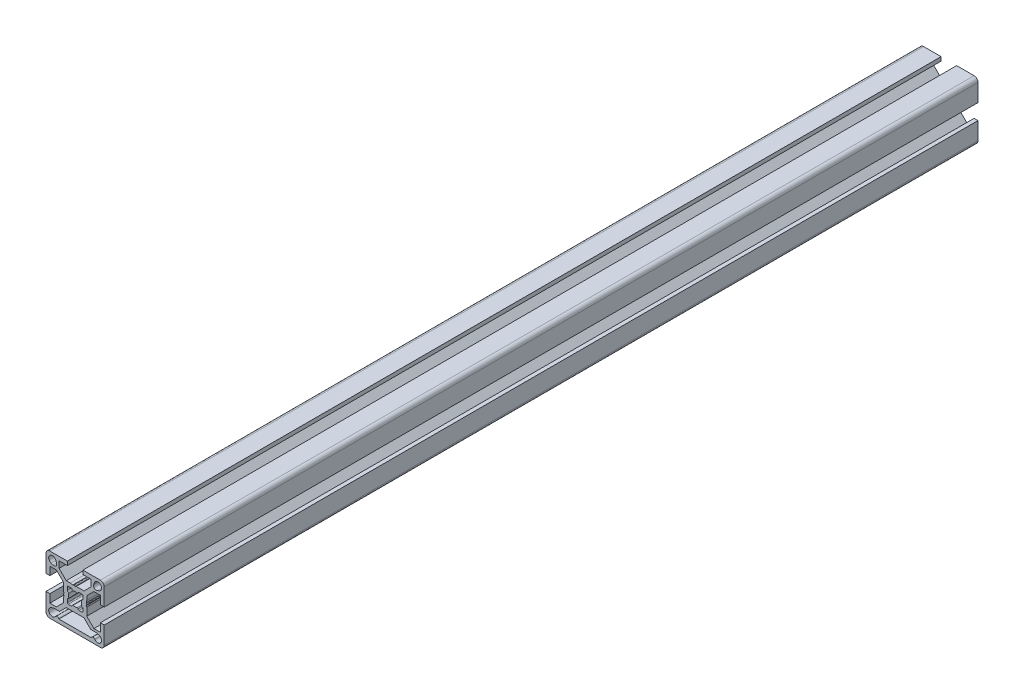
SolidWorks part; units mm, degrees
material "6063-T5"
ref_plane "Piano frontale" through (0, 0, 0) normal (0, 0, 1) x (1, 0, 0)
ref_plane "Piano superiore" through (0, 0, 0) normal (0, 1, 0) x (1, 0, 0)
ref_plane "Piano destro" through (0, 0, 0) normal (1, 0, 0) x (0, 0, -1)
ref_plane "Piano1" through (0, 0, -450) normal (0, 0, -1) x (-1, 0, 0)
sketch "Schizzo1" plane through (0, 0, -450) normal (0, 0, -1) x (-1, 0, 0)
  line L0 (12.3498, 9.9146) -> (11.3422, 9.5479)
  line L1 (9.5479, 11.3422) -> (9.9146, 12.3498)
  line L2 (-4.58, -6) -> (4.58, -6)
  line L3 (8.03, -9.45) -> (11.1, -9.45)
  line L4 (11.1, -9.45) -> (12.3619, -9.919)
  line L5 (8.3553, -13) -> (-8.3553, -13)
  line L6 (-12.3619, -9.919) -> (-11.1, -9.45)
  line L7 (-11.1, -9.45) -> (-8.03, -9.45)
  line L8 (-11.3422, 9.5479) -> (-12.3498, 9.9146)
  line L9 (-9.9146, 12.3498) -> (-9.5479, 11.3422)
  line L10 (4, 3.5) -> (4, 2)
  line L11 (4, -2) -> (4, -3.5)
  line L12 (3.5, -4) -> (2, -4)
  line L13 (-2, -4) -> (-3.5, -4)
  line L14 (-4, -3.5) -> (-4, -2)
  line L15 (-4, 2) -> (-4, 3.5)
  line L16 (-3.5, 4) -> (-2, 4)
  line L17 (2, 4) -> (3.5, 4)
  line L18 (-15, -4) -> (-15, -13)
  line L19 (-13, -15) -> (13, -15)
  line L20 (15, -13) -> (15, -4)
  line L21 (15, -4) -> (13, -4)
  line L22 (13, -4) -> (13, -8.25)
  line L23 (13, -8.25) -> (9.6642, -8.25)
  line L24 (6, -4.5858) -> (6, -2.5)
  line L25 (6, -2.5) -> (5.751, -1.2189)
  line L26 (5.751, -1.2189) -> (5.933, -0.9036)
  line L27 (5.933, -0.4036) -> (5.7, 0)
  line L28 (5.7, 0) -> (5.933, 0.4036)
  line L29 (6, 0.6536) -> (6, 4.5858)
  line L30 (9.6642, 8.25) -> (13, 8.25)
  line L31 (13, 8.25) -> (13, 4)
  line L32 (13, 4) -> (15, 4)
  line L33 (15, 4) -> (15, 13)
  line L34 (13, 15) -> (4, 15)
  line L35 (4, 15) -> (4, 13)
  line L36 (4, 13) -> (8.25, 13)
  line L37 (8.25, 13) -> (8.25, 9.6642)
  line L38 (4.5858, 6) -> (2.5, 6)
  line L39 (2.5, 6) -> (1.2189, 5.751)
  line L40 (1.2189, 5.751) -> (0.9036, 5.933)
  line L41 (0.4036, 5.933) -> (0, 5.7)
  line L42 (0, 5.7) -> (-0.4036, 5.933)
  line L43 (-0.6536, 6) -> (-4.5858, 6)
  line L44 (-8.25, 9.6642) -> (-8.25, 13)
  line L45 (-8.25, 13) -> (-4, 13)
  line L46 (-4, 13) -> (-4, 15)
  line L47 (-4, 15) -> (-13, 15)
  line L48 (-15, 13) -> (-15, 4)
  line L49 (-15, 4) -> (-13, 4)
  line L50 (-13, 4) -> (-13, 8.25)
  line L51 (-13, 8.25) -> (-9.6642, 8.25)
  line L52 (-6, 4.5858) -> (-6, 2.5)
  line L53 (-6, 2.5) -> (-5.751, 1.2189)
  line L54 (-5.751, 1.2189) -> (-5.933, 0.9036)
  line L55 (-5.933, 0.4036) -> (-5.7, 0)
  line L56 (-5.7, 0) -> (-5.933, -0.4036)
  line L57 (-6, -0.6536) -> (-6, -4.5858)
  line L58 (-9.6642, -8.25) -> (-13, -8.25)
  line L59 (-13, -8.25) -> (-13, -4)
  line L60 (-13, -4) -> (-15, -4)
  arc A0 (9.9146, 12.3498) -> (12.3498, 9.9146) centre (11.7, 11.7) cw
  arc A1 (11.3422, 9.5479) -> (9.5479, 11.3422) centre (10.8634, 10.8634) cw
  arc A2 (12.3619, -9.919) -> (10.1276, -12.7665) centre (11.7, -11.7) cw
  arc A3 (10.1276, -12.7665) -> (8.3553, -13) centre (9.3, -13.3279) ccw
  arc A4 (-8.3553, -13) -> (-10.1276, -12.7665) centre (-9.3, -13.3279) ccw
  arc A5 (-10.1276, -12.7665) -> (-12.3619, -9.919) centre (-11.7, -11.7) cw
  arc A6 (-12.3498, 9.9146) -> (-9.9146, 12.3498) centre (-11.7, 11.7) cw
  arc A7 (-9.5479, 11.3422) -> (-11.3422, 9.5479) centre (-10.8634, 10.8634) cw
  arc A8 (4, 2) -> (3.5746, 1.5056) centre (3.5, 2) cw
  arc A9 (3.5746, 1.5056) -> (3.2517, 0.9932) centre (3.6342, 1.1101) ccw
  arc A10 (3.2517, 0.9932) -> (3.2517, -0.9932) centre (0, 0) cw
  arc A11 (3.2517, -0.9932) -> (3.5746, -1.5056) centre (3.6342, -1.1101) ccw
  arc A12 (3.5746, -1.5056) -> (4, -2) centre (3.5, -2) cw
  arc A13 (4, -3.5) -> (3.5, -4) centre (3.5, -3.5) cw
  arc A14 (2, -4) -> (1.5056, -3.5746) centre (2, -3.5) cw
  arc A15 (1.5056, -3.5746) -> (0.9932, -3.2517) centre (1.1101, -3.6342) ccw
  arc A16 (0.9932, -3.2517) -> (-0.9932, -3.2517) centre (0, 0) cw
  arc A17 (-0.9932, -3.2517) -> (-1.5056, -3.5746) centre (-1.1101, -3.6342) ccw
  arc A18 (-1.5056, -3.5746) -> (-2, -4) centre (-2, -3.5) cw
  arc A19 (-3.5, -4) -> (-4, -3.5) centre (-3.5, -3.5) cw
  arc A20 (-4, -2) -> (-3.5746, -1.5056) centre (-3.5, -2) cw
  arc A21 (-3.5746, -1.5056) -> (-3.2517, -0.9932) centre (-3.6342, -1.1101) ccw
  arc A22 (-3.2517, -0.9932) -> (-3.2517, 0.9932) centre (0, 0) cw
  arc A23 (-3.2517, 0.9932) -> (-3.5746, 1.5056) centre (-3.6342, 1.1101) ccw
  arc A24 (-3.5746, 1.5056) -> (-4, 2) centre (-3.5, 2) cw
  arc A25 (-4, 3.5) -> (-3.5, 4) centre (-3.5, 3.5) cw
  arc A26 (-2, 4) -> (-1.5056, 3.5746) centre (-2, 3.5) cw
  arc A27 (-1.5056, 3.5746) -> (-0.9932, 3.2517) centre (-1.1101, 3.6342) ccw
  arc A28 (-0.9932, 3.2517) -> (0.9932, 3.2517) centre (0, 0) cw
  arc A29 (0.9932, 3.2517) -> (1.5056, 3.5746) centre (1.1101, 3.6342) ccw
  arc A30 (1.5056, 3.5746) -> (2, 4) centre (2, 3.5) cw
  arc A31 (3.5, 4) -> (4, 3.5) centre (3.5, 3.5) cw
  arc A32 (-15, -13) -> (-13, -15) centre (-13, -13) ccw
  arc A33 (13, -15) -> (15, -13) centre (13, -13) ccw
  arc A34 (5.933, -0.9036) -> (5.933, -0.4036) centre (5.5, -0.6536) ccw
  arc A35 (5.933, 0.4036) -> (6, 0.6536) centre (5.5, 0.6536) ccw
  arc A36 (15, 13) -> (13, 15) centre (13, 13) ccw
  arc A37 (0.9036, 5.933) -> (0.4036, 5.933) centre (0.6536, 5.5) ccw
  arc A38 (-0.4036, 5.933) -> (-0.6536, 6) centre (-0.6536, 5.5) ccw
  arc A39 (-13, 15) -> (-15, 13) centre (-13, 13) ccw
  arc A40 (-5.933, 0.9036) -> (-5.933, 0.4036) centre (-5.5, 0.6536) ccw
  arc A41 (-5.933, -0.4036) -> (-6, -0.6536) centre (-5.5, -0.6536) ccw
  spline S0 degree 3 poles (4.58, -6) (5.73, -7.15) (6.88, -8.3) (8.03, -9.45) knots 0 0 0 0 1 1 1 1
  spline S1 degree 3 poles (-8.03, -9.45) (-6.88, -8.3) (-5.73, -7.15) (-4.58, -6) knots 0 0 0 0 1 1 1 1
  spline S2 degree 3 poles (9.6642, -8.25) (8.4428, -7.0286) (7.2214, -5.8072) (6, -4.5858) knots 0 0 0 0 1 1 1 1
  spline S3 degree 3 poles (6, 4.5858) (7.2214, 5.8072) (8.4428, 7.0286) (9.6642, 8.25) knots 0 0 0 0 1 1 1 1
  spline S4 degree 3 poles (8.25, 9.6642) (7.0286, 8.4428) (5.8072, 7.2214) (4.5858, 6) knots 0 0 0 0 1 1 1 1
  spline S5 degree 3 poles (-4.5858, 6) (-5.8072, 7.2214) (-7.0286, 8.4428) (-8.25, 9.6642) knots 0 0 0 0 1 1 1 1
  spline S6 degree 3 poles (-9.6642, 8.25) (-8.4428, 7.0286) (-7.2214, 5.8072) (-6, 4.5858) knots 0 0 0 0 1 1 1 1
  spline S7 degree 3 poles (-6, -4.5858) (-7.2214, -5.8072) (-8.4428, -7.0286) (-9.6642, -8.25) knots 0 0 0 0 1 1 1 1
extrude "Estrusione-Estrusione1" add sketch "Schizzo1" against normal blind 450
